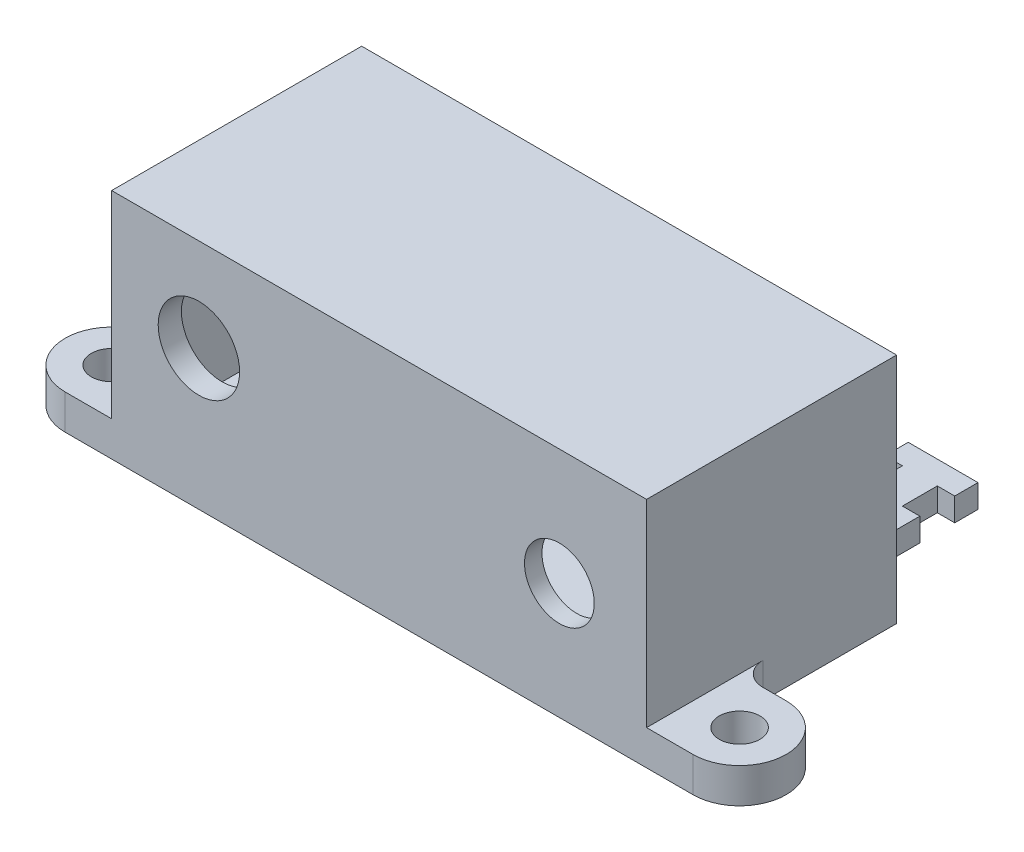
SolidWorks part; units mm, degrees
ref_plane "Спереди" through (0, 0, 0) normal (0, 0, 1) x (1, 0, 0)
ref_plane "Сверху" through (0, 0, 0) normal (0, 1, 0) x (1, 0, 0)
ref_plane "Справа" through (0, 0, 0) normal (1, 0, 0) x (0, 0, -1)
sketch "Эскиз1" plane through (0, 0, 0) normal (0, 0, 1) x (1, 0, 0)
  line L0 (2, 18) -> (2, 2) construction
  line L1 (0, 0) -> (46, 0)
  line L2 (0, 0) -> (0, 20)
  line L3 (0, 20) -> (46, 20)
  line L4 (46, 0) -> (46, 20)
  line L5 (2, 2) -> (44, 2) construction
  line L6 (44, 2) -> (44, 18) construction
  line L7 (44, 18) -> (2, 18) construction
  line L8 (23, 2) -> (23, 0) construction
  line L9 (38.5, 18) -> (38.5, 2) construction
  line L10 (44, 10) -> (46, 10) construction
  circle A0 centre (7.5, 12) radius 3.5
  circle A1 centre (38.5, 10) radius 3
  dimension "D5" = 10
  dimension "D6" = 7
  dimension "D8" = 5.5
  dimension "D9" = 6
  dimension "D1" = 42
  dimension "D2" = 16
  dimension "D3" = 20
  dimension "D4" = 46
  dimension "D7" = 5.5
extrude "Бобышка-Вытянуть1" add sketch "Эскиз1" along normal blind 1.5
sketch "Эскиз2" plane through (0, 0, 0) normal (0, 0, -1) x (-1, 0, 0)
  circle A0 centre (-7.5, 12) radius 3.5
  circle A1 centre (-7.5, 12) radius 5
  dimension "D1" = 10
  dimension "D2" = 7
extrude "Бобышка-Вытянуть2" add sketch "Эскиз2" along normal blind 0.5
sketch "Эскиз3" plane through (0, 0, 0) normal (0, 0, -1) x (-1, 0, 0)
  line L1 (0, 0) -> (-46, 0)
  line L2 (0, 0) -> (0, 20)
  line L3 (0, 20) -> (-46, 20)
  line L4 (-46, 0) -> (-46, 20)
  line L5 (-44.5, 18.5) -> (-1, 18.5)
  line L6 (-44.5, 18.5) -> (-44.5, 2)
  line L7 (-44.5, 2) -> (-1, 2)
  line L8 (-1, 18.5) -> (-1, 2)
  dimension "D1" = 2
  dimension "D2" = 1
  dimension "D3" = 1.5
  dimension "D4" = 1.5
extrude "Бобышка-Вытянуть3" add sketch "Эскиз3" along normal blind 20
sketch "Эскиз4" plane through (0, 0, 0) normal (0, -1, 0) x (1, 0, 0)
  line L0 (0, 1.5) -> (-4, 1.5)
  line L1 (0, 1.5) -> (0, -6.5)
  line L2 (-4, -6.5) -> (0, -6.5)
  line L3 (0, 1.5) -> (0, -20) construction
  line L4 (50, 1.5) -> (46, 1.5)
  line L5 (50, -6.5) -> (46, -6.5)
  line L6 (46, 1.5) -> (46, -20) construction
  line L7 (46, 1.5) -> (46, -6.5)
  arc A0 (-4, 1.5) -> (-4, -6.5) centre (-4, -2.5) ccw
  arc A1 (50, -6.5) -> (50, 1.5) centre (50, -2.5) ccw
  circle A2 centre (-4, -2.5) radius 1.75
  circle A3 centre (50, -2.5) radius 1.75
  dimension "D1" = 4
  dimension "D2" = 3.5
  dimension "D3" = 4
  dimension "D4" = 4
extrude "Бобышка-Вытянуть4" add sketch "Эскиз4" against normal blind 3
fillet "Скругление1" radius 2 2 edges at (0, 1.5, -6.5) (46, 1.5, -6.5)
sketch "Эскиз5" plane through (0, 0, 0) normal (0, -1, 0) x (1, 0, 0)
  line L0 (46, -20) -> (0, -20) construction
  line L1 (41, -20) -> (35, -20)
  line L2 (41, -20) -> (41, -27)
  line L3 (41, -32) -> (35, -32)
  line L4 (35, -20) -> (35, -27)
  line L5 (46, -8.5) -> (46, -20) construction
  line L6 (11, -20) -> (5, -20)
  line L7 (11, -20) -> (11, -27)
  line L8 (11, -32) -> (5, -32)
  line L9 (5, -20) -> (5, -27)
  line L10 (0, -8.5) -> (0, -20) construction
  line L11 (5, -30) -> (5, -32)
  line L12 (5, -30) -> (6.5, -30)
  line L13 (11, -30) -> (11, -32)
  line L14 (5, -27) -> (6.5, -27)
  line L15 (6.5, -30) -> (6.5, -27)
  line L16 (11, -30) -> (9.5, -30)
  line L17 (35, -30) -> (35, -32)
  line L18 (11, -27) -> (9.5, -27)
  line L19 (9.5, -30) -> (9.5, -27)
  line L20 (35, -30) -> (36.5, -30)
  line L21 (41, -30) -> (41, -32)
  line L22 (35, -27) -> (36.5, -27)
  line L23 (36.5, -30) -> (36.5, -27)
  line L24 (41, -30) -> (39.5, -30)
  line L26 (41, -27) -> (39.5, -27)
  line L27 (39.5, -30) -> (39.5, -27)
  point P30 (0, 0)
  point P31 (7.2502, -30.321)
  dimension "D1" = 5
  dimension "D2" = 5
  dimension "D3" = 6
  dimension "D4" = 12
  dimension "D5" = 2
  dimension "D6" = 3
  dimension "D7" = 1.5
extrude "Бобышка-Вытянуть5" add sketch "Эскиз5" against normal blind 2
fillet "Скругление2" radius 2 4 edges at (5, 1, -20) (35, 1, -20) (11, 1, -20) (41, 1, -20)
